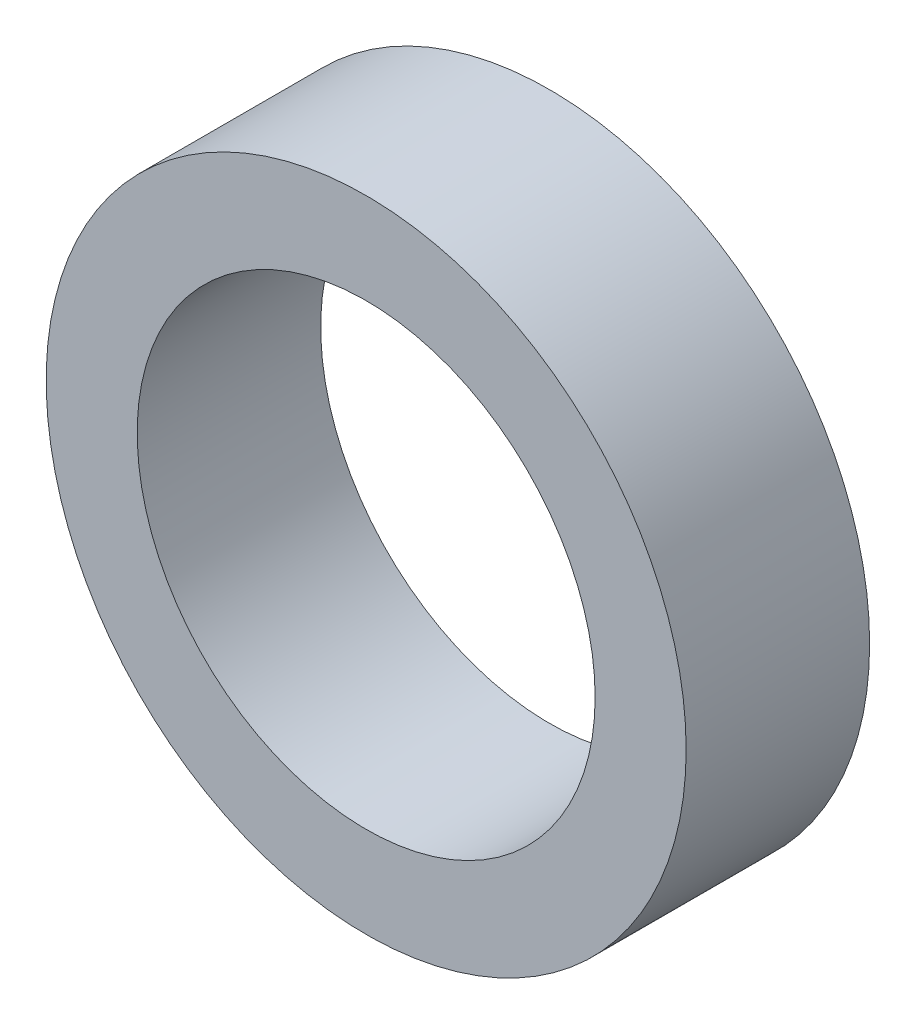
SolidWorks part; units mm, degrees
material "Acrylic (Medium-high impact)"
ref_plane "Front Plane" through (0, 0, 0) normal (0, 0, 1) x (1, 0, 0)
ref_plane "Top Plane" through (0, 0, 0) normal (0, 1, 0) x (1, 0, 0)
ref_plane "Right Plane" through (0, 0, 0) normal (1, 0, 0) x (0, 0, -1)
sketch "Sketch1" plane through (0, 0, 0) normal (0, 0, 1) x (1, 0, 0)
  circle A0 centre (0, 0) radius 15.85
  circle A1 centre (0, 0) radius 22.15
extrude "Boss-Extrude1" add sketch "Sketch1" along normal blind 12.7
